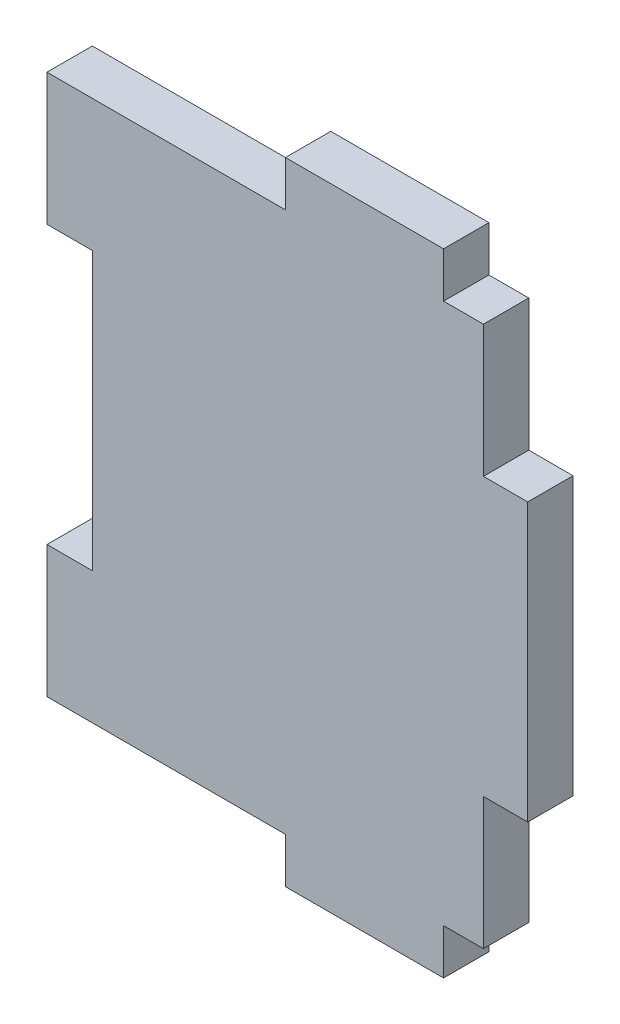
SolidWorks part; units mm, degrees
ref_plane "Front Plane" through (0, 0, 0) normal (0, 0, 1) x (1, 0, 0)
ref_plane "Top Plane" through (0, 0, 0) normal (0, 1, 0) x (1, 0, 0)
ref_plane "Right Plane" through (0, 0, 0) normal (1, 0, 0) x (0, 0, -1)
sketch "Sketch1" plane through (0, 0, 0) normal (0, 0, 1) x (1, 0, 0)
  line L1 (-26.289, 32.5755) -> (26.289, 32.5755)
  line L2 (-26.289, 32.5755) -> (-26.289, -32.5755)
  line L3 (-26.289, -32.5755) -> (26.289, -32.5755)
  line L4 (26.289, 32.5755) -> (26.289, -32.5755)
  line L5 (-26.289, 32.5755) -> (26.289, -32.5755) construction
  line L6 (-26.289, -32.5755) -> (26.289, 32.5755) construction
  line L7 (-20.828, -16.7005) -> (-26.289, -16.7005)
  line L8 (-20.828, -16.7005) -> (-20.828, 16.7005)
  line L9 (-20.828, 16.7005) -> (-26.289, 16.7005)
  line L10 (-26.289, -16.7005) -> (-26.289, 16.7005)
  line L11 (-20.828, -16.7005) -> (-26.289, 16.7005) construction
  line L12 (-20.828, 16.7005) -> (-26.289, -16.7005) construction
  line L13 (31.623, -16.7005) -> (26.289, -16.7005)
  line L14 (31.623, -16.7005) -> (31.623, 16.7005)
  line L15 (31.623, 16.7005) -> (26.289, 16.7005)
  line L16 (26.289, -16.7005) -> (26.289, 16.7005)
  line L17 (31.623, -16.7005) -> (26.289, 16.7005) construction
  line L18 (31.623, 16.7005) -> (26.289, -16.7005) construction
  point P0 (0, 0)
  point P6 (-23.5585, 0)
  point P11 (28.956, 0)
  point P16 (0, 0)
  dimension "D1" = 5.461
  dimension "D2" = 5.334
  dimension "D3" = 52.578
  dimension "D4" = 15.875
  dimension "D5" = 65.151
extrude "Boss-Extrude1" add sketch "Sketch1" along normal blind 5.461 contours L9 L8 L7 L2 L3 L4 L1 | L14 L15 L4 L13
sketch "Sketch2" plane through (0, 0, 5.461) normal (0, 0, 1) x (1, 0, 0)
  line L0 (-26.289, 32.5755) -> (26.289, 32.5755) construction
  line L1 (21.4884, 32.5755) -> (2.4384, 32.5755)
  line L2 (21.4884, 32.5755) -> (21.4884, 38.0365)
  line L3 (21.4884, 38.0365) -> (2.4384, 38.0365)
  line L4 (2.4384, 32.5755) -> (2.4384, 38.0365)
  line L5 (-26.289, -32.5755) -> (26.289, -32.5755) construction
  line L6 (21.4884, -32.5755) -> (2.4384, -32.5755)
  line L7 (21.4884, -32.5755) -> (21.4884, -38.0365)
  line L8 (21.4884, -38.0365) -> (2.4384, -38.0365)
  line L9 (2.4384, -32.5755) -> (2.4384, -38.0365)
  line L10 (26.289, 32.5755) -> (26.289, 16.7005) construction
  dimension "D1" = 5.461
  dimension "D2" = 4.8006
  dimension "D3" = 19.05
extrude "Boss-Extrude2" add sketch "Sketch2" against normal up to surface (5.461 mm away) up to face at (1.7992, 0, 0)
